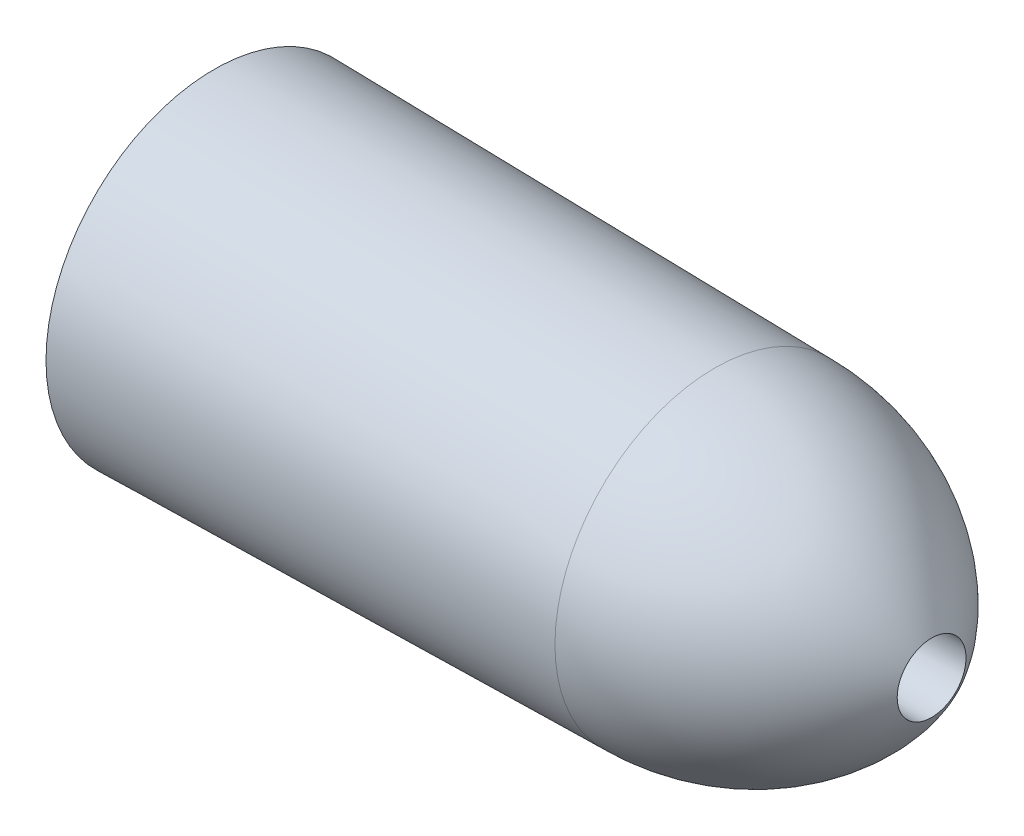
SolidWorks part; units mm, degrees
ref_plane "Front Plane" through (0, 0, 0) normal (0, 0, 1) x (1, 0, 0)
ref_plane "Top Plane" through (0, 0, 0) normal (0, 1, 0) x (1, 0, 0)
ref_plane "Right Plane" through (0, 0, 0) normal (1, 0, 0) x (0, 0, -1)
sketch "Sketch1" plane through (0, 0, 0) normal (0, 1, 0) x (1, 0, 0)
  line L0 (-491.5391, 0) -> (314.3706, 0) construction
  line L1 (-273.05, -63.9803) -> (-273.05, 63.9803)
  line L2 (-273.05, -12.3) -> (-273.05, 12.3)
  line L3 (0, -13.1) -> (0, 13.1)
  line L4 (-273.05, 12.3) -> (0, 13.1)
  line L5 (0, -13.1) -> (-273.05, -12.3)
  line L6 (-82.55, -60.7972) -> (-82.55, 60.7972)
  line L7 (-273.05, 63.9803) -> (-82.55, 60.7972)
  line L8 (-273.05, -63.9803) -> (-82.55, -60.7972)
  arc A0 (-82.55, 60.7972) -> (0, 13.1) centre (-82.55, -34.4865) cw
  arc A1 (-82.55, -60.7972) -> (0, -13.1) centre (-82.55, 34.4865) ccw
  point P6 (-273.05, 0)
  point P9 (-273.05, 0)
  point P12 (0, 0)
  point P15 (-82.55, 0)
  point P17 (-82.55, -12.8581)
  point P18 (-82.55, 12.8581)
  dimension "D1" = 127.9606
  dimension "D2" = 273.05
  dimension "D3" = 24.6
  dimension "D4" = 26.2
  dimension "D5" = 190.5
  dimension "D6" = 121.5944
revolve "Revolve1" add sketch "Sketch1" angle 360 about L0
